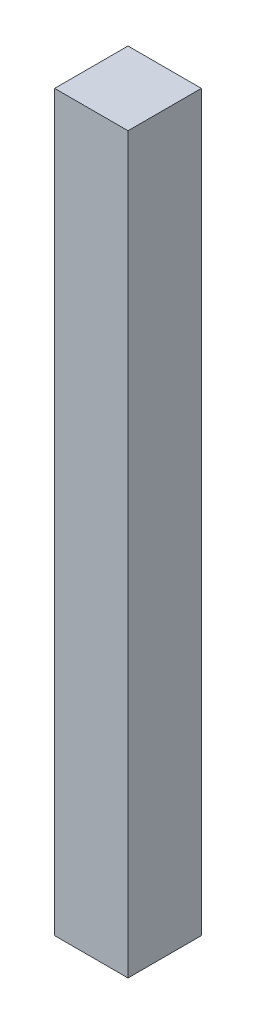
SolidWorks part; units mm, degrees
ref_plane "Ebene vorne" through (0, 0, 0) normal (0, 0, 1) x (1, 0, 0)
ref_plane "Ebene oben" through (0, 0, 0) normal (0, 1, 0) x (1, 0, 0)
ref_plane "Ebene rechts" through (0, 0, 0) normal (1, 0, 0) x (0, 0, -1)
sketch "Skizze1" plane through (0, 0, 0) normal (0, 1, 0) x (1, 0, 0)
  line L1 (0, 0) -> (20, 0)
  line L2 (0, 0) -> (0, -20)
  line L3 (0, -20) -> (20, -20)
  line L4 (20, 0) -> (20, -20)
  dimension "D1" = 20
extrude "Aufsatz-Linear austragen1" add sketch "Skizze1" along normal blind 200
